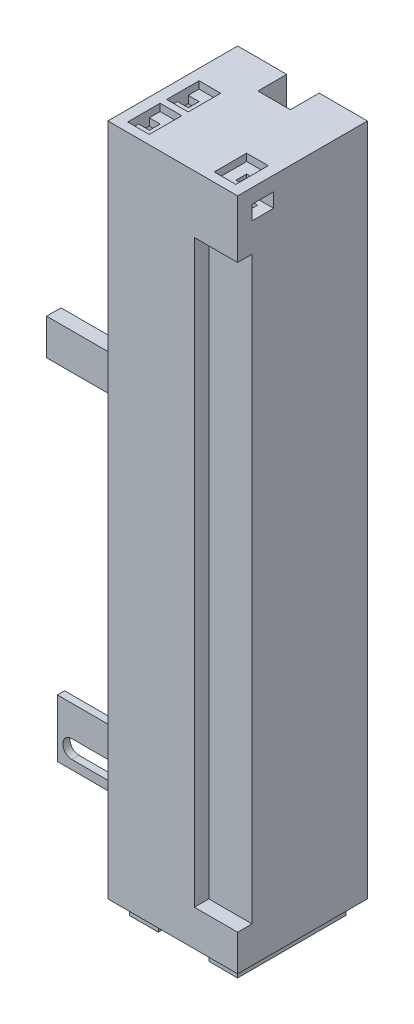
SolidWorks part; units mm, degrees
ref_plane "Front Plane" through (0, 0, 0) normal (0, 0, 1) x (1, 0, 0)
ref_plane "Top Plane" through (0, 0, 0) normal (0, 1, 0) x (1, 0, 0)
ref_plane "Right Plane" through (0, 0, 0) normal (1, 0, 0) x (0, 0, -1)
sketch "Sketch1" plane through (0, 0, 0) normal (0, 1, 0) x (1, 0, 0)
  line L1 (0, 0) -> (36, 0)
  line L2 (0, 0) -> (0, 36)
  line L3 (0, 36) -> (36, 36)
  line L4 (36, 0) -> (36, 36)
  dimension "D1" = 36
  dimension "D2" = 36
extrude "Boss-Extrude1" add sketch "Sketch1" along normal blind 186.9
sketch "Sketch2" plane through (0, 0, 0) normal (0, -1, 0) x (1, 0, 0)
  line L0 (0, 0) -> (36, 0) construction
  line L1 (3, -3) -> (7, -3)
  line L2 (3, -3) -> (3, -33)
  line L3 (3, -33) -> (7, -33)
  line L4 (7, -11) -> (7, -25)
  line L5 (36, -36) -> (0, -36) construction
  line L6 (0, -36) -> (0, 0) construction
  line L20 (36, 0) -> (36, -36) construction
  line L29 (7, -3) -> (11, -3)
  line L31 (7, -11) -> (11, -11)
  line L32 (11, -3) -> (11, -11)
  line L33 (7, -25) -> (11, -25)
  line L35 (7, -33) -> (11, -33)
  line L36 (11, -25) -> (11, -33)
  line L45 (29, -3) -> (33, -3)
  line L46 (29, -11) -> (29, -25)
  line L47 (29, -33) -> (33, -33)
  line L48 (33, -3) -> (33, -33)
  line L50 (29, -3) -> (25, -3)
  line L52 (29, -11) -> (25, -11)
  line L53 (25, -3) -> (25, -11)
  line L54 (29, -33) -> (25, -33)
  line L56 (29, -25) -> (25, -25)
  line L57 (25, -33) -> (25, -25)
  dimension "D1" = 3
  dimension "D2" = 3
  dimension "D3" = 3
  dimension "D4" = 4
  dimension "D5" = 4
  dimension "D6" = 8
  dimension "D7" = 8
  dimension "D8" = 4
  dimension "D9" = 3
  dimension "D10" = 3
  dimension "D11" = 3
  dimension "D12" = 4
  dimension "D13" = 4
  dimension "D14" = 4
extrude "Boss-Extrude2" add sketch "Sketch2" along normal blind 4
sketch "Sketch3" plane through (0, 0, 0) normal (0, -1, 0) x (1, 0, 0)
  line L0 (36, -36) -> (0, -36) construction
  line L2 (0, -36) -> (0, 0) construction
  circle A0 centre (18, -18) radius 2
  dimension "D1" = 4
  dimension "D2" = 18
  dimension "D3" = 18
extrude "Cut-Extrude1" cut sketch "Sketch3" against normal blind 5
sketch "Sketch4" plane through (0, 0, -36) normal (0, 0, 1) x (1, 0, 0)
  line L0 (0, 186.9) -> (36, 186.9) construction
  line L1 (13.62, 186.9) -> (22.62, 186.9)
  line L2 (13.62, 186.9) -> (13.62, 0)
  line L3 (13.62, 0) -> (22.62, 0)
  line L4 (22.62, 186.9) -> (22.62, 0)
  line L5 (0, 0) -> (36, 0) construction
  line L7 (36, 186.9) -> (36, 0) construction
  dimension "D1" = 13.38
  dimension "D2" = 9
extrude "Cut-Extrude2" cut sketch "Sketch4" along normal blind 8
sketch "Sketch5" plane through (36, 0, 0) normal (1, 0, 0) x (0, 0, -1)
  line L0 (0, 186.9) -> (36, 186.9) construction
  line L1 (4, 182.9) -> (10, 182.9)
  line L2 (4, 182.9) -> (4, 178.9)
  line L3 (4, 178.9) -> (10, 178.9)
  line L4 (10, 182.9) -> (10, 178.9)
  line L5 (0, 186.9) -> (0, 0) construction
  dimension "D1" = 6
  dimension "D2" = 4
  dimension "D3" = 4
  dimension "D4" = 4
extrude "Cut-Extrude3" cut sketch "Sketch5" against normal blind 9
sketch "Sketch6" plane through (0, 186.9, 0) normal (0, 1, 0) x (1, 0, 0)
  line L0 (36, 0) -> (36, 36) construction
  line L1 (30, 8.5) -> (33, 8.5)
  line L2 (30, 8.5) -> (30, 5.5)
  line L3 (30, 5.5) -> (33, 5.5)
  line L4 (33, 8.5) -> (33, 5.5)
  line L5 (0, 0) -> (36, 0) construction
  dimension "D1" = 3
  dimension "D2" = 3
  dimension "D3" = 3
  dimension "D4" = 5.5
extrude "Cut-Extrude4" cut sketch "Sketch6" against normal blind 10
sketch "Sketch7" plane through (0, 0, 0) normal (-1, 0, 0) x (0, 0, 1)
  line L0 (-36, 186.9) -> (-36, 0) construction
  line L1 (-28, 0) -> (-26, 0)
  line L2 (-28, 0) -> (-28, 16)
  line L3 (-28, 16) -> (-26, 16)
  line L4 (-26, 0) -> (-26, 16)
  dimension "D1" = 2
  dimension "D2" = 16
  dimension "D3" = 8
extrude "Boss-Extrude3" add sketch "Sketch7" along normal blind 40
sketch "Sketch8" plane through (0, 0, -26) normal (0, 0, 1) x (1, 0, 0)
  line L0 (-40, 0) -> (0, 0) construction
  line L1 (-40, 0) -> (-40, 16) construction
  line L3 (-36, 7.5) -> (-12, 7.5)
  line L5 (-36, 2.5) -> (-12, 2.5)
  arc A0 (-36, 7.5) -> (-36, 2.5) centre (-36, 5) ccw
  arc A1 (-12, 2.5) -> (-12, 7.5) centre (-12, 5) ccw
  dimension "D1" = 5
  dimension "D2" = 5
  dimension "D4" = 5
  dimension "D3" = 4
  dimension "D5" = 5
  dimension "D6" = 24
extrude "Cut-Extrude5" cut sketch "Sketch8" against normal up to next
sketch "Sketch9" plane through (0, 0, 0) normal (-1, 0, 0) x (0, 0, 1)
  line L0 (-26, 0) -> (0, 0) construction
  line L1 (-32, 103.5) -> (-28, 103.5)
  line L2 (-32, 103.5) -> (-32, 93.5)
  line L3 (-32, 93.5) -> (-28, 93.5)
  line L4 (-28, 103.5) -> (-28, 93.5)
  line L5 (-36, 186.9) -> (-36, 0) construction
  dimension "D1" = 103.5
  dimension "D2" = 10
  dimension "D3" = 4
  dimension "D4" = 4
extrude "Boss-Extrude4" add sketch "Sketch9" along normal blind 45
chamfer "Chamfer1" distance 20 angle 45 2 edges at (0, 93.5, -30) (0, 16, -27)
sketch "Sketch10" plane through (0, 0, -26) normal (0, 0, 1) x (1, 0, 0)
  line L0 (-17.1716, 93.5) -> (-2, 78.3284)
  line L1 (-2, 78.3284) -> (-2, 93.5)
  line L2 (-2, 93.5) -> (-17.1716, 93.5)
  line L3 (0, 186.9) -> (0, 0) construction
  line L4 (-20, 93.5) -> (0, 73.5) construction
  line L5 (-45, 93.5) -> (-20, 93.5) construction
  line L6 (-17.1716, 16) -> (-2, 31.1716)
  line L7 (-2, 31.1716) -> (-2, 16)
  line L8 (-2, 16) -> (-17.1716, 16)
  line L9 (0, 36) -> (-20, 16) construction
  line L10 (-40, 16) -> (-20, 16) construction
  dimension "D1" = 2
  dimension "D2" = 2
  dimension "D3" = 0
  dimension "D4" = 2
  dimension "D5" = 2
  dimension "D6" = 0
extrude "Cut-Extrude6" cut sketch "Sketch10" along direction (0, 0, -1) on the side against the normal blind 27
sketch "Sketch11" plane through (0, 0, 0) normal (-1, 0, 0) x (0, 0, 1)
  line L0 (-36, 186.9) -> (0, 186.9) construction
  line L1 (-4, 182.9) -> (-10, 182.9)
  line L2 (-4, 182.9) -> (-4, 178.9)
  line L3 (-4, 178.9) -> (-10, 178.9)
  line L4 (-10, 182.9) -> (-10, 178.9)
  line L5 (0, 186.9) -> (0, 0) construction
  line L7 (-14.8, 182.9) -> (-20.8, 182.9)
  line L8 (-14.8, 182.9) -> (-14.8, 178.9)
  line L9 (-14.8, 178.9) -> (-20.8, 178.9)
  line L10 (-20.8, 182.9) -> (-20.8, 178.9)
  line L11 (-16, 172.9) -> (-10, 172.9)
  line L12 (-16, 172.9) -> (-16, 166.9)
  line L13 (-16, 166.9) -> (-10, 166.9)
  line L14 (-10, 172.9) -> (-10, 166.9)
  dimension "D1" = 6
  dimension "D2" = 4
  dimension "D3" = 4
  dimension "D4" = 4
  dimension "D5" = 6
  dimension "D6" = 4.8
  dimension "D7" = 6
  dimension "D8" = 6
  dimension "D9" = 6
  dimension "D10" = 6
  dimension "D11" = 4
extrude "Cut-Extrude7" cut sketch "Sketch11" against normal blind 9
sketch "Sketch12" plane through (0, 186.9, 0) normal (0, 1, 0) x (1, 0, 0)
  line L0 (0, 0) -> (36, 0) construction
  line L1 (3, 8.5) -> (6, 8.5)
  line L2 (3, 8.5) -> (3, 5.5)
  line L3 (3, 5.5) -> (6, 5.5)
  line L4 (6, 8.5) -> (6, 5.5)
  line L5 (0, 36) -> (0, 0) construction
  line L7 (6, 16.3) -> (3, 16.3)
  line L8 (6, 16.3) -> (6, 19.3)
  line L9 (6, 19.3) -> (3, 19.3)
  line L10 (3, 16.3) -> (3, 19.3)
  dimension "D1" = 3
  dimension "D2" = 3
  dimension "D3" = 5.5
  dimension "D4" = 3
  dimension "D5" = 3
  dimension "D6" = 3
  dimension "D7" = 7.8
extrude "Cut-Extrude8" cut sketch "Sketch12" against normal blind 10
sketch "Sketch13" plane through (0, 0, 0) normal (0, 0, 1) x (1, 0, 0)
  line L0 (36, 186.9) -> (36, 0) construction
  line L1 (24, 170.9) -> (36, 170.9)
  line L2 (24, 170.9) -> (24, 10)
  line L3 (24, 10) -> (36, 10)
  line L4 (36, 170.9) -> (36, 10)
  line L5 (0, 186.9) -> (36, 186.9) construction
  line L6 (0, 0) -> (36, 0) construction
  dimension "D1" = 12
  dimension "D2" = 16
  dimension "D3" = 10
extrude "Cut-Extrude9" cut sketch "Sketch13" against normal blind 4
sketch "Sketch14" plane through (0, 186.9, 0) normal (0, 1, 0) x (1, 0, 0)
  line L0 (33, 5.5) -> (33, 8.5) construction
  line L1 (33, 11.5) -> (27, 11.5)
  line L2 (33, 11.5) -> (33, 2.5)
  line L3 (33, 2.5) -> (27, 2.5)
  line L4 (27, 11.5) -> (27, 2.5)
  line L5 (33, 8.5) -> (30, 8.5) construction
  line L6 (30, 5.5) -> (33, 5.5) construction
  line L7 (30, 8.5) -> (30, 5.5) construction
  line L8 (3, 19.3) -> (3, 16.3) construction
  line L9 (3, 22.3) -> (9, 22.3)
  line L10 (3, 22.3) -> (3, 13.3)
  line L11 (3, 13.3) -> (9, 13.3)
  line L12 (9, 22.3) -> (9, 13.3)
  line L13 (3, 11.5) -> (9, 11.5)
  line L14 (3, 11.5) -> (3, 2.5)
  line L15 (3, 2.5) -> (9, 2.5)
  line L16 (9, 11.5) -> (9, 2.5)
  line L17 (3, 8.5) -> (3, 5.5) construction
  line L18 (6, 8.5) -> (3, 8.5) construction
  line L19 (3, 5.5) -> (6, 5.5) construction
  line L20 (6, 5.5) -> (6, 8.5) construction
  line L21 (3, 16.3) -> (6, 16.3) construction
  line L22 (6, 16.3) -> (6, 19.3) construction
  line L23 (6, 19.3) -> (3, 19.3) construction
  dimension "D1" = 0
  dimension "D2" = 3
  dimension "D3" = 3
  dimension "D4" = 3
  dimension "D5" = 0
  dimension "D6" = 0
  dimension "D7" = 3
  dimension "D8" = 3
  dimension "D9" = 3
  dimension "D10" = 3
  dimension "D11" = 3
  dimension "D12" = 3
extrude "Cut-Extrude10" cut sketch "Sketch14" against normal blind 2
